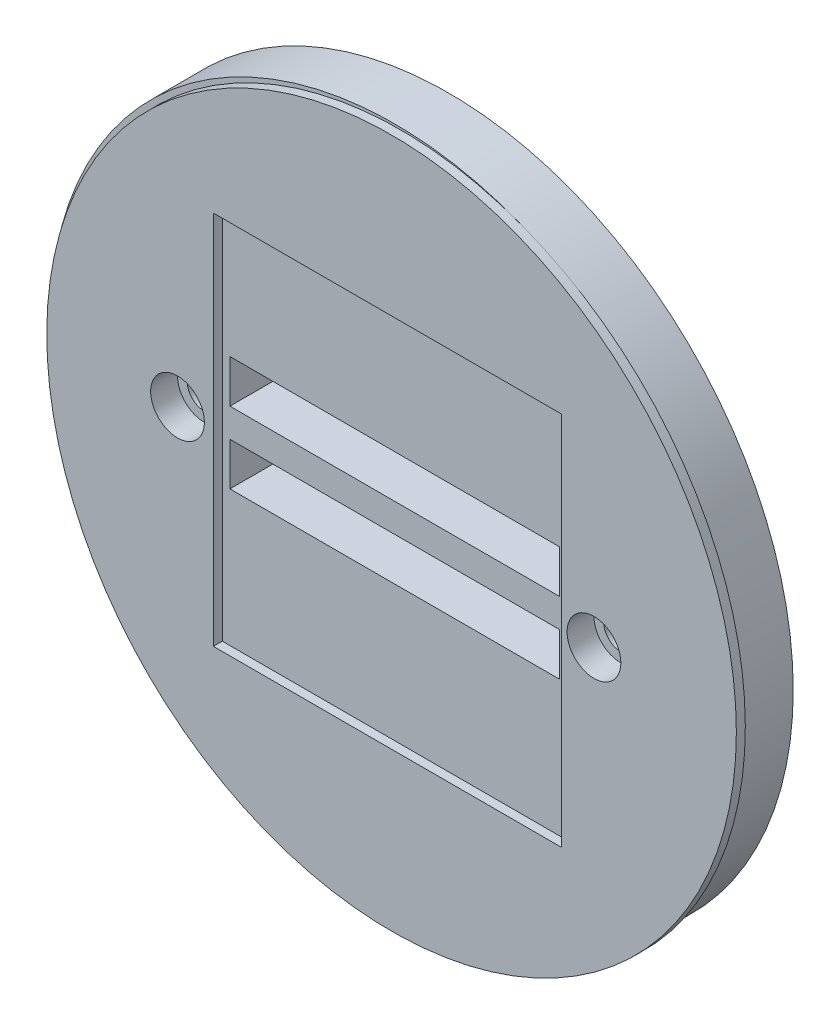
SolidWorks part; units mm, degrees
material "ABS"
ref_plane "Front Plane" through (0, 0, 0) normal (0, 0, 1) x (1, 0, 0)
ref_plane "Top Plane" through (0, 0, 0) normal (0, 1, 0) x (1, 0, 0)
ref_plane "Right Plane" through (0, 0, 0) normal (1, 0, 0) x (0, 0, -1)
sketch "Sketch1" plane through (0, 0, 0) normal (0, 0, 1) x (1, 0, 0)
  line L0 (18.4, 6.8) -> (18.4, 2)
  line L2 (-18.4, 6.8) -> (18.4, 6.8)
  line L3 (18.4, -1.2) -> (-18.4, -1.2)
  line L4 (-18.4, 2) -> (-18.4, 6.8)
  line L5 (-18.4, -1.2) -> (-18.4, -6)
  line L6 (-18.4, -6) -> (18.4, -6)
  line L7 (18.4, -6) -> (18.4, -1.2)
  line L8 (18.4, 2) -> (-18.4, 2)
  circle A0 centre (-23.25, 0) radius 1.925
  circle A1 centre (0, 0) radius 34.7 construction
  circle A2 centre (23.25, 0) radius 1.925
  circle A6 centre (0, 0) radius 38.5
  dimension "D2" = 69.4
  dimension "D3" = 18.4
  dimension "D6" = 18.4
  dimension "D7" = 23.25
  dimension "D4" = 23.25
  dimension "D5" = 77
  dimension "D9" = 4.8
  dimension "D10" = 3.85
  dimension "D8" = 3.85
extrude "Main Flange Coupling" add sketch "Sketch1" against normal blind 6
sketch "Sketch2" plane through (0, 0, 0) normal (0, 0, 1) x (1, 0, 0)
  line L0 (-19.25, 20.75) -> (19.65, 20.75)
  line L1 (-19.25, 20.75) -> (-19.25, -21.15)
  line L2 (-19.25, -21.15) -> (19.65, -21.15)
  line L3 (19.65, 20.75) -> (19.65, -21.15)
  line L4 (-19.25, 20.75) -> (19.65, -21.15) construction
  line L5 (-19.25, -21.15) -> (19.65, 20.75) construction
  circle A0 centre (0.65, -0.25) radius 38.5
  circle A1 centre (-23.25, 0) radius 1.7
  circle A2 centre (23.25, 0) radius 1.7
  dimension "D3" = 77
  dimension "D4" = 3.4
  dimension "D5" = 3.4
  dimension "D1" = 38.9
  dimension "D2" = 41.9
  dimension "D6" = 21
  dimension "D7" = 19
extrude "Boss-Extrude1" add sketch "Sketch2" along normal blind 1
sketch "Sketch3" plane through (0, 0, 1) normal (0, 0, 1) x (1, 0, 0)
  circle A0 centre (-23.25, 0) radius 3
  circle A1 centre (23.25, 0) radius 3
  dimension "D1" = 6
  dimension "D2" = 6
extrude "Cut-Extrude1" cut sketch "Sketch3" against normal blind 3
equation "\"D4@Sketch2\"= 3 + \"tol1@parametersSketch@prostheticParameters.SLDPRT\""
equation "\"D5@Sketch2\"= 3 + \"tol1@parametersSketch@prostheticParameters.SLDPRT\""
equation "\"D1@Sketch2\"= 38.5 + \"tol2@parametersSketch@prostheticParameters.SLDPRT\""
equation "\"D2@Sketch2\"= 41.5 + \"tol2@parametersSketch@prostheticParameters.SLDPRT\""
equation "\"D8@Sketch1\"= 3.45 + \"tol1@parametersSketch@prostheticParameters.SLDPRT\""
equation "\"D10@Sketch1\"= 3.45 + \"tol1@parametersSketch@prostheticParameters.SLDPRT\""
equation "\"D3@Sketch1\"= 18 + \"tol2@parametersSketch@prostheticParameters.SLDPRT\""
equation "\"D6@Sketch1\" = 18 + \"tol2@parametersSketch@prostheticParameters.SLDPRT\""
equation "\"D9@Sketch1\"= 4 + \"tol2@parametersSketch@prostheticParameters.SLDPRT\" * 2"
